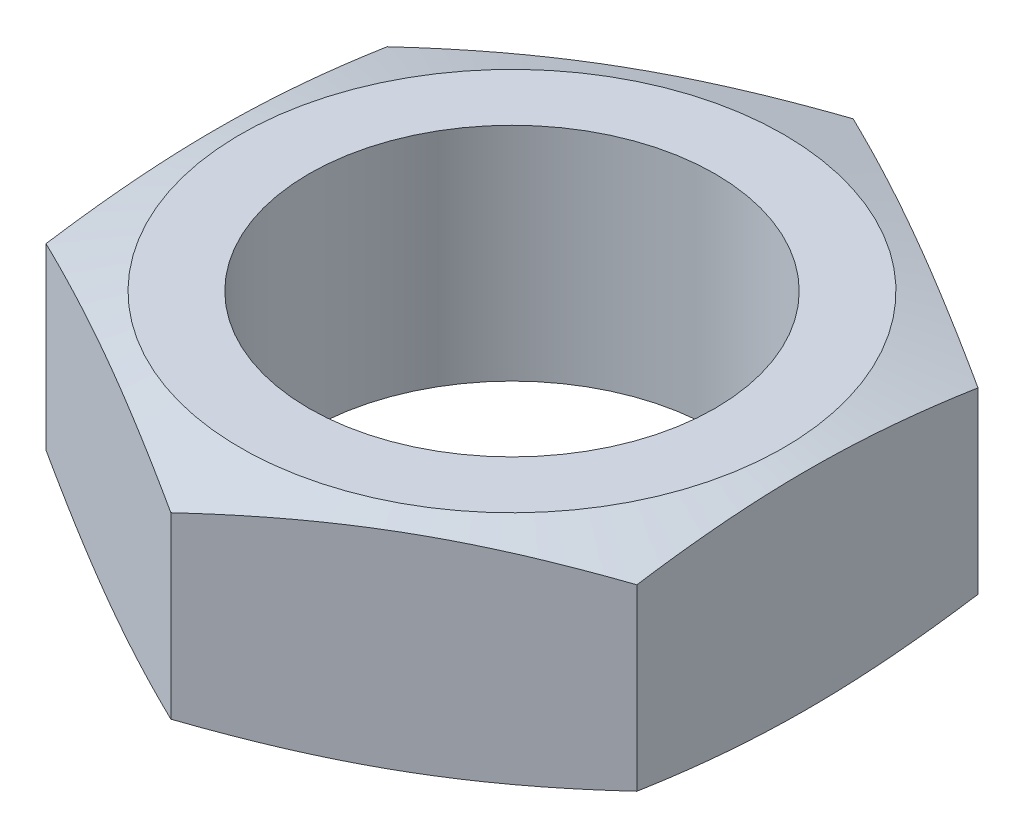
SolidWorks part; units mm, degrees
ref_plane "Front Plane" through (0, 0, 0) normal (0, 0, 1) x (1, 0, 0)
ref_plane "Top Plane" through (0, 0, 0) normal (0, 1, 0) x (1, 0, 0)
ref_plane "Right Plane" through (0, 0, 0) normal (1, 0, 0) x (0, 0, -1)
sketch "Sketch1" plane through (0, 0, 0) normal (0, 1, 0) x (1, 0, 0)
  line L0 (0, 0) -> (0, 3.6662) construction
  line L1 (0, -3.6662) -> (3.175, -1.8331)
  line L2 (3.175, -1.8331) -> (3.175, 1.8331)
  line L3 (3.175, 1.8331) -> (0, 3.6662)
  line L4 (0, 3.6662) -> (-3.175, 1.8331)
  line L5 (-3.175, 1.8331) -> (-3.175, -1.8331)
  line L6 (-3.175, -1.8331) -> (0, -3.6662)
  circle A0 centre (0, 0) radius 3.175 construction
  circle A1 centre (0, 0) radius 2.1828
  dimension "D2" = 4.3656
  dimension "D1" = 6.35
extrude "Boss-Extrude1" add sketch "Sketch1" along normal blind 2.3813
sketch "Sketch2" plane through (0, 0, 0) normal (1, 0, 0) x (0, 0, -1)
  line L0 (2.9182, 2.3813) -> (3.6662, 2.1515)
  line L1 (1.8331, 2.3813) -> (3.6662, 2.3813) construction
  line L2 (3.6662, 2.3813) -> (3.6662, 0) construction
  line L3 (3.6662, 2.1515) -> (3.6662, 2.3813)
  line L4 (3.6662, 2.3813) -> (2.9182, 2.3813)
  line L5 (2.9182, 2.3813) -> (2.9182, 0) construction
  line L6 (1.8331, 0) -> (3.6662, 0) construction
  line L7 (2.9182, 0) -> (3.6662, 0)
  line L8 (3.6662, 0) -> (3.6662, 0.2298)
  line L9 (3.6662, 0.2298) -> (2.9182, 0)
  line L10 (0, 0) -> (0, 2.3813) construction
  line L11 (-1.8331, 2.3813) -> (1.8331, 2.3813) construction
revolve "Cut-Revolve1" cut sketch "Sketch2" angle 360 about L10
